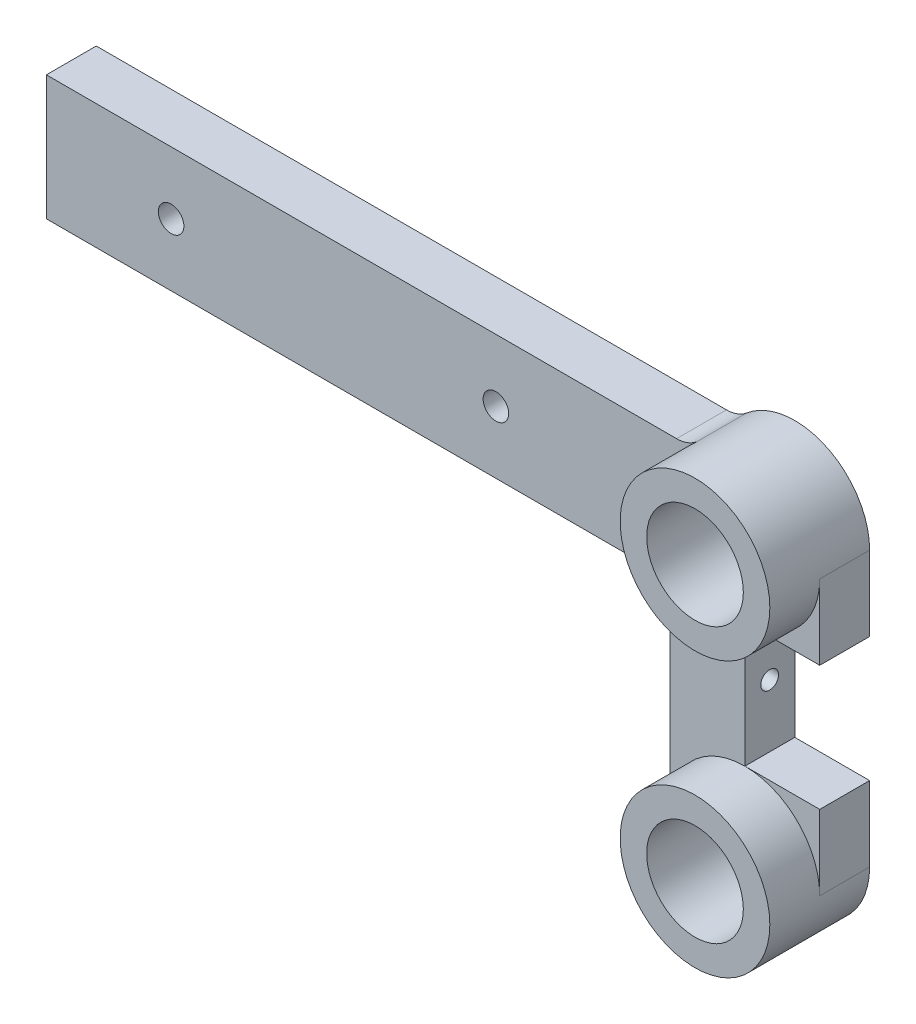
SolidWorks part; units mm, degrees
ref_plane "Plan de face" through (0, 0, 0) normal (0, 0, 1) x (1, 0, 0)
ref_plane "Plan de dessus" through (0, 0, 0) normal (0, 1, 0) x (1, 0, 0)
ref_plane "Plan de droite" through (0, 0, 0) normal (1, 0, 0) x (0, 0, -1)
ref_plane "Plan1" through (0, 0, 8) normal (0, 0, 1) x (1, 0, 0)
sketch "Esquisse1" plane through (0, 0, 8) normal (0, 0, 1) x (1, 0, 0)
  line L0 (-12, 44) -> (-12, 0)
  line L1 (12, 0) -> (12, 12)
  line L2 (12, 12) -> (0, 12)
  line L3 (0, 12) -> (0, 32)
  line L4 (0, 32) -> (12, 32)
  line L5 (12, 32) -> (12, 44)
  arc A0 (12, 44) -> (-12, 44) centre (0, 44) ccw
  arc A1 (-12, 0) -> (12, 0) centre (0, 0) ccw
extrude "Boss.-Extru.1" add sketch "Esquisse1" against normal blind 8
sketch "Esquisse2" plane through (-12, 0, 0) normal (-1, 0, 0) x (0, 0, 1)
  line L1 (0, 52) -> (8, 52)
  line L2 (0, 52) -> (0, 32)
  line L3 (0, 32) -> (8, 32)
  line L4 (8, 52) -> (8, 32)
  line L5 (8, -55) -> (8, 55) construction
  line L6 (0, 44) -> (0, 0) construction
  dimension "D1" = 20
extrude "Boss.-Extru.2" add sketch "Esquisse2" along normal blind 100 and the other way blind 5
sketch "Esquisse3" plane through (0, 0, 8) normal (0, 0, 1) x (1, 0, 0)
  circle A0 centre (0, 44) radius 12
extrude "Boss.-Extru.3" add sketch "Esquisse3" along normal blind 8
sketch "Esquisse4" plane through (0, 0, 8) normal (0, 0, 1) x (1, 0, 0)
  circle A0 centre (0, 0) radius 12
extrude "Boss.-Extru.4" add sketch "Esquisse4" along normal blind 8
hole_wizard "Diamètre du perçage Ø4.1 (4.1)1" positions "Esquisse6" profile "Esquisse5" hole size "Ø4.1" standard "Ansi Metric" end condition through all
sketch "Esquisse6" plane through (0, 0, 8) normal (0, 0, 1) x (1, 0, 0)
  line L0 (-92, 42) -> (-39.9238, 42) construction
  line L2 (-112, 32) -> (-112, 52) construction
  point P0 (-39.9238, 42)
  point P1 (-92, 42)
  point P12 (-65.9619, 42)
  point P13 (-112, 42)
  dimension "D1" = 52.0762
  dimension "D2" = 20
sketch "Esquisse5" plane through (-39.9238, 42, 8) normal (1, 0, 0) x (0, -1, 0)
  line L0 (0, 0) -> (0, 8)
  line L1 (0, 8) -> (2.05, 8)
  line L2 (2.05, 8) -> (2.05, 0)
  line L5 (2.05, 0) -> (0, 0)
  line L11 (0, -6.35) -> (0, 107.95) construction
  dimension "Diamètre du perçage jusqu'au prochain" = 4.1
  dimension "Profondeur du perçage jusqu'au prochain" = 8
hole_wizard "Diamètre du perçage Ø15.5 (15.5)1" positions "Esquisse8" profile "Esquisse7" hole size "Ø15.5" standard "Ansi Metric"
sketch "Esquisse8" plane through (0, 0, 16) normal (0, 0, 1) x (1, 0, 0)
  point P0 (0, 44)
  point P1 (0, 0)
sketch "Esquisse7" plane through (0, 44, 16) normal (1, 0, 0) x (0, -1, 0)
  line L0 (0, 0) -> (0, 16)
  line L1 (0, 16) -> (7.75, 16)
  line L2 (7.75, 16) -> (7.75, 0)
  line L5 (7.75, 0) -> (0, 0)
  line L11 (0, -6.35) -> (0, 107.95) construction
  dimension "Diamètre du perçage jusqu'au prochain" = 15.5
  dimension "Profondeur du perçage jusqu'au prochain" = 16
hole_wizard "Dégagement M2.51" positions "Esquisse10" profile "Esquisse9" hole size "M2.5" standard "Ansi Metric"
sketch "Esquisse10" plane through (0, 0, 0) normal (1, 0, 0) x (0, 0, -1)
  point P0 (-4.03, 22)
sketch "Esquisse9" plane through (0, 22, 4.03) normal (0, 1, 0) x (0, 0, -1)
  line L0 (0, 0) -> (0, 10)
  line L1 (0, 10) -> (1.425, 10)
  line L2 (1.425, 10) -> (1.425, 0)
  line L5 (1.425, 0) -> (0, 0)
  line L10 (0, 10) -> (-1.425, 10) construction
  line L11 (0, -6.35) -> (0, 107.95) construction
  dimension "Diamètre du perçage" = 2.85
  dimension "Profondeur du perçage" = 10
  dimension "Angle de pointe" = 180
fillet "Congé1" radius 5 2 edges at (-12, 32, 4) (-8.9443, 52, 4)
